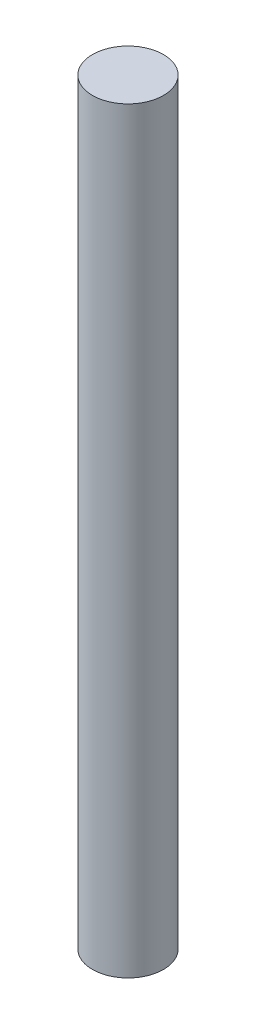
SolidWorks part; units mm, degrees
ref_plane "Front Plane" through (0, 0, 0) normal (0, 0, 1) x (1, 0, 0)
ref_plane "Top Plane" through (0, 0, 0) normal (0, 1, 0) x (1, 0, 0)
ref_plane "Right Plane" through (0, 0, 0) normal (1, 0, 0) x (0, 0, -1)
sketch "Sketch1" plane through (0, 0, 0) normal (0, 1, 0) x (1, 0, 0)
  circle A0 centre (0, 0) radius 4.7625
  dimension "D1" = 9.525
extrude "Boss-Extrude1" add sketch "Sketch1" along normal mid plane 101.6
